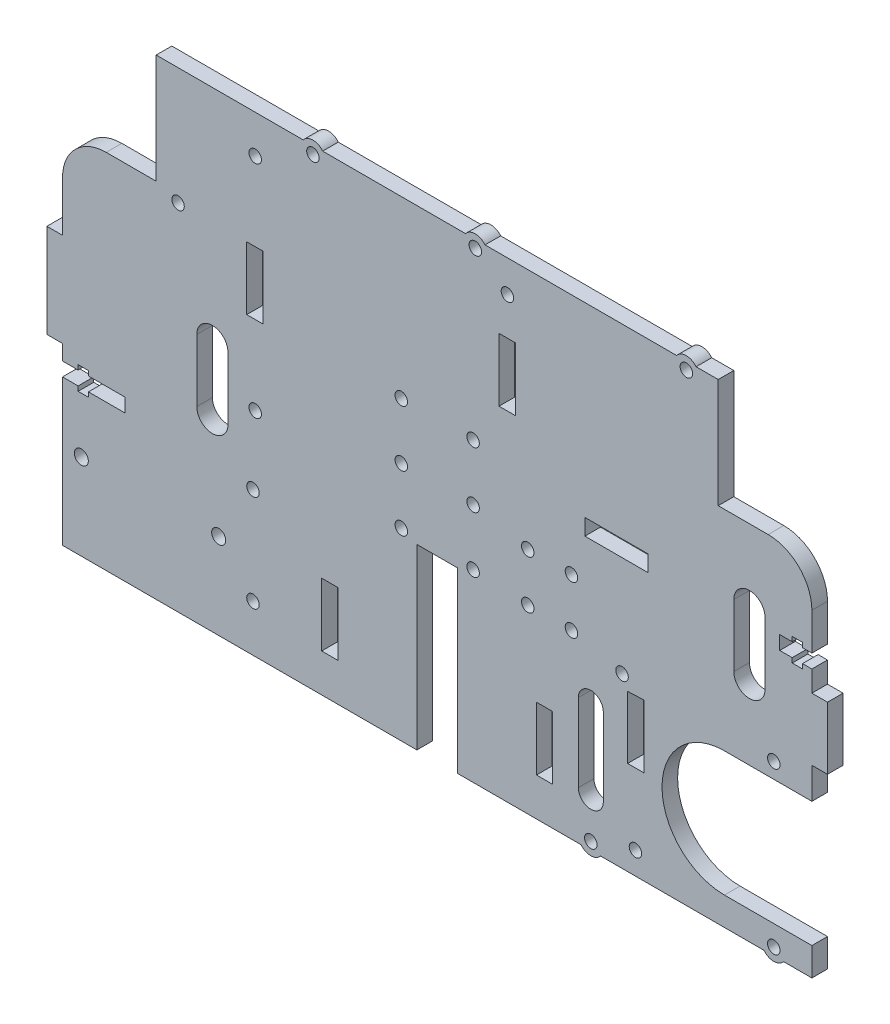
SolidWorks part; units mm, degrees
ref_plane "Front Plane" through (0, 0, 0) normal (0, 0, 1) x (1, 0, 0)
ref_plane "Top Plane" through (0, 0, 0) normal (0, 1, 0) x (1, 0, 0)
ref_plane "Right Plane" through (0, 0, 0) normal (1, 0, 0) x (0, 0, -1)
sketch "Sketch1" plane through (0, 0, 0) normal (0, 0, 1) x (1, 0, 0)
  line L1 (-120, 75.5) -> (120, 75.5)
  line L2 (-120, 75.5) -> (-120, -75.5)
  line L3 (-120, -75.5) -> (120, -75.5)
  line L4 (120, 75.5) -> (120, -75.5)
  dimension "D1" = 120
  dimension "D2" = 240
  dimension "D3" = 151
  dimension "D4" = 75.5
extrude "Boss-Extrude1" add sketch "Sketch1" along normal blind 5
sketch "Sketch2" plane through (0, 0, 0) normal (0, 0, -1) x (-1, 0, 0)
  line L0 (0, 0) -> (0, 57.3071) construction
  line L1 (0, 0) -> (-98.1862, 0) construction
  line L2 (-120, 75.5) -> (120, 75.5) construction
  line L3 (-60, 75.5) -> (50, 75.5)
  line L4 (-60, 75.5) -> (-60, 24.5)
  line L5 (-60, 24.5) -> (50, 24.5)
  line L6 (50, 75.5) -> (50, 24.5)
  dimension "D1" = 60
  dimension "D2" = 50
  dimension "D3" = 51
extrude "Cut-Extrude1" [suppressed] cut sketch "Sketch2" against normal blind 10
sketch "Sketch3" plane through (0, 0, 0) normal (0, 0, -1) x (-1, 0, 0)
  line L0 (0, 0) -> (0, -78.8573) construction
  line L2 (6.5, -75.5) -> (6.5, -18.5)
  line L3 (120, -75.5) -> (-120, -75.5) construction
  line L4 (-6.5, -75.5) -> (-6.5, -18.5)
  line L5 (6.5, -18.5) -> (-6.5, -18.5)
  line L6 (6.5, -75.5) -> (-6.5, -75.5)
  dimension "D1" = 6.5
  dimension "D2" = 6.5
  dimension "D3" = 57
extrude "Cut-Extrude2" cut sketch "Sketch3" against normal blind 10
sketch "Sketch5" plane through (0, 0, 0) normal (0, 0, -1) x (-1, 0, 0)
  line L0 (0, 0) -> (-50.5193, 0) construction
  line L1 (-31.8, -43.1) -> (-31.8, -63.3)
  line L2 (0, 0) -> (0, -33.9855) construction
  line L3 (-31.8, -43.1) -> (-37, -43.1)
  line L5 (-37, -43.1) -> (-37, -63.3)
  line L7 (-31.8, -63.3) -> (-37, -63.3)
  line L16 (31.8, -63.3) -> (37, -63.3)
  line L17 (37, -43.1) -> (37, -63.3)
  line L18 (31.8, -43.1) -> (37, -43.1)
  line L19 (31.8, -43.1) -> (31.8, -63.3)
  dimension "D1" = 5.2
  dimension "D2" = 20.2
  dimension "D3" = 37
  dimension "D4" = 43.1
extrude "Cut-Extrude4" cut sketch "Sketch5" against normal blind 10
sketch "Sketch6" plane through (0, 0, 0) normal (0, 0, -1) x (-1, 0, 0)
  line L0 (0, 0) -> (0, 25.6979) construction
  line L1 (0, 0) -> (-29.2256, 0) construction
  circle A1 centre (11.5, 19.5) radius 2
  circle A3 centre (11.5, 1.5) radius 2
  circle A5 centre (11.5, -16.5) radius 2
  circle A6 centre (-11.5, -16.5) radius 2
  circle A7 centre (-11.5, 1.5) radius 2
  circle A8 centre (-11.5, 19.5) radius 2
  dimension "D1" = 4
  dimension "D2" = 4
  dimension "D3" = 4
  dimension "D4" = 11.5
  dimension "D5" = 19.5
  dimension "D6" = 18
  dimension "D7" = 18
extrude "Cut-Extrude5" cut sketch "Sketch6" against normal blind 10
sketch "Sketch7" plane through (0, 0, 0) normal (0, 0, -1) x (-1, 0, 0)
  line L0 (0, 0) -> (0, -14.6108) construction
  line L1 (-36, -2.1) -> (-36, -21.1184) construction
  line L2 (0, 0) -> (-17.8652, 0) construction
  circle A1 centre (-43, -2.1) radius 2
  circle A3 centre (-43, -17.6) radius 2
  circle A8 centre (-29, -17.6) radius 2
  circle A9 centre (-29, -2.1) radius 2
  dimension "D3" = 4
  dimension "D4" = 4
  dimension "D5" = 15.5
  dimension "D6" = 4.2
  dimension "D1" = 36
  dimension "D2" = 7
extrude "Cut-Extrude6" cut sketch "Sketch7" against normal blind 10
sketch "Sketch8" plane through (0, 0, 0) normal (0, 0, -1) x (-1, 0, 0)
  line L0 (-120, -26.5) -> (-92, -26.5)
  line L1 (-120, -75.5) -> (-120, 75.5) construction
  line L2 (-120, -66.5) -> (-92, -66.5)
  line L3 (-6.5, -75.5) -> (-120, -75.5) construction
  line L4 (-120, -26.5) -> (-120, -66.5)
  arc A0 (-92, -26.5) -> (-92, -66.5) centre (-92, -46.5) cw
  dimension "D1" = 28
  dimension "D2" = 40
  dimension "D3" = 9
extrude "Cut-Extrude7" cut sketch "Sketch8" against normal blind 10
sketch "Sketch9" plane through (0, 0, 0) normal (0, 0, -1) x (-1, 0, 0)
  line L1 (0, 0) -> (-30.7701, 0) construction
  line L3 (0, 0) -> (0, -53.9951) construction
  circle A0 centre (-59.2, -21.5) radius 2
  circle A1 centre (-107.8, -21.5) radius 2
  circle A2 centre (-49.2, -73) radius 2
  circle A3 centre (-107.8, -73) radius 2
  dimension "D1" = 4
  dimension "D2" = 4
  dimension "D3" = 4
  dimension "D4" = 4
  dimension "D7" = 48.6
  dimension "D10" = 58.6
  dimension "D5" = 59.2
  dimension "D6" = 21.5
  dimension "D8" = 49.2
  dimension "D9" = 73
extrude "Cut-Extrude8" cut sketch "Sketch9" against normal blind 10
sketch "Sketch10" plane through (0, 0, 0) normal (0, 0, -1) x (-1, 0, 0)
  circle A0 centre (-107.8, -73) radius 2
  circle A1 centre (-107.8, -73) radius 4
  circle A2 centre (-49.2, -73) radius 2
  circle A3 centre (-49.2, -73) radius 4
  dimension "D1" = 4
  dimension "D2" = 8
  dimension "D3" = 4
  dimension "D4" = 8
extrude "Boss-Extrude2" add sketch "Sketch10" against normal blind 5
sketch "Sketch11" plane through (0, 0, 5) normal (0, 0, 1) x (1, 0, 0)
  line L1 (0, 0) -> (0, 50.8583) construction
  line L5 (0, 0) -> (-51.0189, 0) construction
  circle A0 centre (-24.8, 29.5) radius 2
  circle A1 centre (24.8, 29.5) radius 2
  dimension "D1" = 4
  dimension "D2" = 4
  dimension "D4" = 29.5
  dimension "D3" = 24.8
  dimension "D5" = 24.8
extrude "Cut-Extrude9" [suppressed] cut sketch "Sketch11" against normal blind 10
sketch "Sketch12" plane through (0, 0, 0) normal (0, 0, -1) x (-1, 0, 0)
  line L0 (-49.2, -35.1071) -> (-49.2, -60.1071) construction
  line L1 (-45.2, -35.1071) -> (-45.2, -60.1071)
  line L2 (-53.2, -35.1071) -> (-53.2, -60.1071)
  line L3 (-49.2, -71) -> (-49.2, -25.3616) construction
  arc A0 (-45.2, -35.1071) -> (-53.2, -35.1071) centre (-49.2, -35.1071) ccw
  arc A1 (-53.2, -60.1071) -> (-45.2, -60.1071) centre (-49.2, -60.1071) ccw
  circle A2 centre (-49.2, -73) radius 2 construction
  point P2 (-49.2, -47.6071)
  dimension "D1" = 8
  dimension "D2" = 25
extrude "Cut-Extrude10" cut sketch "Sketch12" against normal blind 10
sketch "Sketch13" plane through (0, 0, 0) normal (0, 0, -1) x (-1, 0, 0)
  line L0 (0, 0) -> (0, 120.0783) construction
  line L1 (-120, 75.5) -> (-90, 75.5)
  line L2 (-120, 75.5) -> (-120, 40.5)
  line L3 (-120, 40.5) -> (-90, 40.5)
  line L4 (-90, 75.5) -> (-90, 40.5)
  line L5 (90, 75.5) -> (90, 40.5)
  line L6 (120, 40.5) -> (90, 40.5)
  line L7 (120, 75.5) -> (120, 40.5)
  line L8 (120, 75.5) -> (90, 75.5)
  dimension "D1" = 30
  dimension "D2" = 35
extrude "Cut-Extrude11" cut sketch "Sketch13" against normal blind 10
sketch "Sketch14" plane through (0, 0, 0) normal (0, 0, -1) x (-1, 0, 0)
  line L1 (0, 0) -> (0, 60.6425) construction
  line L3 (0, 0) -> (51.7242, 0) construction
  circle A0 centre (-22.5, 65.3) radius 2
  circle A3 centre (-22.5, 20.7) radius 2
  dimension "D1" = 4
  dimension "D2" = 4
  dimension "D9" = 44.6
  dimension "D7" = 22.5
  dimension "D8" = 20.7
extrude "Cut-Extrude12" [suppressed] cut sketch "Sketch14" against normal blind 10
sketch "Sketch16" plane through (0, 0, 0) normal (0, 0, -1) x (-1, 0, 0)
  line L0 (0, 0) -> (67.1487, 0) construction
  line L1 (0, 0) -> (0, -41.5882) construction
  circle A1 centre (59, -29.5) radius 2
  circle A3 centre (59, -60.5) radius 2
  dimension "D1" = 4
  dimension "D2" = 4
  dimension "D5" = 31
  dimension "D3" = 29.5
  dimension "D4" = 59
extrude "Cut-Extrude13" cut sketch "Sketch16" against normal blind 5
sketch "Sketch17" plane through (0, 0, 0) normal (0, 0, -1) x (-1, 0, 0)
  line L0 (-100, 17) -> (-100, -3) construction
  line L1 (-95, 17) -> (-95, -3)
  line L2 (-105, 17) -> (-105, -3)
  line L4 (-120, 7) -> (-88.2409, 7) construction
  line L5 (-120, -26.5) -> (-120, 40.5) construction
  arc A0 (-95, 17) -> (-105, 17) centre (-100, 17) ccw
  arc A1 (-105, -3) -> (-95, -3) centre (-100, -3) ccw
  point P2 (-100, 7)
  dimension "D1" = 10
  dimension "D2" = 20
  dimension "D3" = 15
extrude "Cut-Extrude14" cut sketch "Sketch17" against normal blind 5
sketch "Sketch18" plane through (0, 0, 0) normal (0, 0, -1) x (-1, 0, 0)
  line L0 (72, -15.5) -> (72, 4.5) construction
  line L1 (67, -15.5) -> (67, 4.5)
  line L2 (77, -15.5) -> (77, 4.5)
  line L5 (0, 0) -> (0, 30.7987) construction
  line L6 (0, 0) -> (40.6403, 0) construction
  arc A0 (67, -15.5) -> (77, -15.5) centre (72, -15.5) ccw
  arc A1 (77, 4.5) -> (67, 4.5) centre (72, 4.5) ccw
  point P2 (72, -5.5)
  dimension "D4" = 20
  dimension "D1" = 72
  dimension "D2" = 10
  dimension "D3" = 4.5
extrude "Cut-Extrude15" cut sketch "Sketch18" against normal blind 5
sketch "Sketch19" plane through (0, 0, 0) normal (0, 0, -1) x (-1, 0, 0)
  line L0 (23, 20.5) -> (23, 40.5) construction
  line L1 (18, 20.5) -> (18, 40.5)
  line L2 (28, 20.5) -> (28, 40.5)
  line L5 (0, 0) -> (0, 49.6195) construction
  line L6 (0, 0) -> (50, 0) construction
  arc A0 (18, 20.5) -> (28, 20.5) centre (23, 20.5) ccw
  arc A1 (28, 40.5) -> (18, 40.5) centre (23, 40.5) ccw
  point P2 (23, 30.5)
  dimension "D1" = 10
  dimension "D2" = 23
  dimension "D3" = 20
  dimension "D4" = 20.5
extrude "Cut-Extrude16" [suppressed] cut sketch "Sketch19" against normal blind 10
sketch "Sketch20" plane through (0, 0, 0) normal (0, 0, -1) x (-1, 0, 0)
  line L1 (60.9956, 18) -> (60.9956, 38.2)
  line L3 (60.9956, 18) -> (55.7956, 18)
  line L6 (55.7956, 18) -> (55.7956, 38.2)
  line L7 (60.9956, 38.2) -> (55.7956, 38.2)
  line L8 (0, 0) -> (0, 33.2819) construction
  line L9 (0, 0) -> (33.8288, 0) construction
  dimension "D1" = 18
  dimension "D2" = 5.2
  dimension "D3" = 20.2
  dimension "D4" = 55.7956
extrude "Cut-Extrude17" cut sketch "Sketch20" against normal blind 10
sketch "Sketch21" plane through (0, 0, 0) normal (0, 0, -1) x (-1, 0, 0)
  line L1 (0, 0) -> (0, 47.6704) construction
  line L3 (0, 0) -> (36.5305, 0) construction
  circle A0 centre (58.2956, -7.3) radius 2
  circle A1 centre (58.2956, 63.3) radius 2
  dimension "D1" = 4
  dimension "D2" = 4
  dimension "D3" = 7.3
  dimension "D5" = 58.2956
  dimension "D4" = 58.2956
  dimension "D6" = 63.3
extrude "Cut-Extrude18" cut sketch "Sketch21" against normal blind 10
sketch "Sketch24" plane through (0, 0, 5) normal (0, 0, 1) x (1, 0, 0)
  line L8 (66.2, -45.5) -> (66.1962, -25.3)
  line L9 (66.1962, -25.3) -> (61, -25.5)
  line L10 (61, -25.5) -> (61, -45.5)
  line L11 (61, -45.5) -> (66.2, -45.5)
  dimension "D1" = 5.2
  dimension "D2" = 20.2
extrude "Cut-Extrude20" cut sketch "Sketch24" against normal blind 5
sketch "Sketch25" plane through (0, 0, 0) normal (0, 0, -1) x (-1, 0, 0)
  circle A0 centre (-63.5, -68.3) radius 2
  dimension "D1" = 4
extrude "Cut-Extrude21" cut sketch "Sketch25" against normal blind 5
sketch "Sketch26" plane through (0, 0, 0) normal (0, 0, -1) x (-1, 0, 0)
  circle A0 centre (39.8, 73) radius 2
  circle A1 centre (-12.2, 73) radius 2
  dimension "D1" = 4
  dimension "D2" = 4
extrude "Cut-Extrude22" cut sketch "Sketch26" against normal blind 10
sketch "Sketch27" plane through (0, 0, 0) normal (0, 0, -1) x (-1, 0, 0)
  circle A0 centre (39.8, 73) radius 2
  circle A1 centre (39.8, 73) radius 4
  circle A2 centre (-12.2, 73) radius 4
  circle A3 centre (-12.2, 73) radius 2
  dimension "D1" = 8
  dimension "D2" = 8
  dimension "D3" = 4
  dimension "D4" = 4
extrude "Boss-Extrude4" add sketch "Sketch27" against normal blind 5
fillet "Fillet1" radius 14 2 edges at (120, 40.5, 2.5) (-120, 40.5, 2.5)
sketch "Sketch28" plane through (0, 0, 5) normal (0, 0, 1) x (1, 0, 0)
  line L8 (25, 33) -> (25, 53.2)
  line L9 (25, 53.2) -> (19.8, 53.2)
  line L10 (19.8, 53.2) -> (19.8, 33)
  line L11 (19.8, 33) -> (25, 33)
  dimension "D1" = 20.2
  dimension "D2" = 5.2
extrude "Cut-Extrude23" cut sketch "Sketch28" against normal blind 5
sketch "Sketch29" plane through (0, 0, 5) normal (0, 0, 1) x (1, 0, 0)
  line L8 (47.3, 10.7) -> (67.5, 10.7)
  line L9 (67.5, 10.7) -> (67.5, 15.9)
  line L10 (67.5, 15.9) -> (47.3, 15.9)
  line L11 (47.3, 15.9) -> (47.3, 10.7)
  dimension "D1" = 5.2
  dimension "D2" = 20.2
extrude "Cut-Extrude24" cut sketch "Sketch29" against normal blind 5
sketch "Sketch30" plane through (0, 0, 0) normal (0, 0, -1) x (-1, 0, 0)
  circle A0 centre (-79.8, 73) radius 2
  dimension "D1" = 4
extrude "Cut-Extrude25" cut sketch "Sketch30" against normal blind 5
sketch "Sketch31" plane through (0, 0, 0) normal (0, 0, -1) x (-1, 0, 0)
  circle A0 centre (-79.8, 73) radius 2
  circle A1 centre (-79.8, 73) radius 4
  dimension "D1" = 8
extrude "Boss-Extrude5" add sketch "Sketch31" against normal blind 5
sketch "Sketch32" plane through (0, 0, 0) normal (0, 0, -1) x (-1, 0, 0)
  circle A0 centre (83, 38) radius 2
  dimension "D1" = 4
extrude "Cut-Extrude26" cut sketch "Sketch32" against normal blind 5
sketch "Sketch33" plane through (0, 0, 0) normal (0, 0, -1) x (-1, 0, 0)
  line L0 (120, 26.5) -> (120, -75.5) construction
  line L5 (-120, -26.5) -> (-120, 26.5) construction
  line L6 (120, -19.5) -> (125, -19.5)
  line L7 (120, -19.5) -> (120, 10.5)
  line L8 (120, 10.5) -> (125, 10.5)
  line L9 (125, -19.5) -> (125, 10.5)
  line L10 (-120, 3.5) -> (-125, 3.5)
  line L11 (-120, 3.5) -> (-120, -16.5)
  line L12 (-120, -16.5) -> (-125, -16.5)
  line L13 (-125, 3.5) -> (-125, -16.5)
  line L15 (90, 40.5) -> (106, 40.5) construction
  line L16 (-92, -26.5) -> (-120, -26.5) construction
  dimension "D4" = 30
  dimension "D5" = 30
  dimension "D6" = 5
  dimension "D7" = 5
  dimension "D8" = 10
  dimension "D9" = 20
extrude "Boss-Extrude6" add sketch "Sketch33" against normal blind 5
sketch "Sketch34" plane through (0, 0, 0) normal (0, 0, -1) x (-1, 0, 0)
  circle A1 centre (113.98, -48) radius 2.25
  circle A3 centre (69.98, -48) radius 2.25
extrude "Cut-Extrude27" cut sketch "Sketch34" against normal blind 5
sketch "Sketch35" plane through (0, 0, 0) normal (0, 0, -1) x (-1, 0, 0)
  line L0 (-119.8939, 12.4056) -> (-90.0212, 12.4056) construction
  line L1 (-120, 14.6056) -> (-117, 14.6056)
  line L2 (-117, 14.6056) -> (-117, 16.1056)
  line L3 (-117, 16.1056) -> (-113.7, 16.1056)
  line L4 (-113.7, 16.1056) -> (-113.7, 14.6056)
  line L5 (-113.7, 14.6056) -> (-109.7051, 14.6056)
  line L6 (-109.7051, 14.6056) -> (-109.7051, 10.2056)
  line L7 (-109.7051, 10.2056) -> (-113.7, 10.2056)
  line L8 (-113.7, 10.2056) -> (-113.7, 8.7056)
  line L9 (-113.7, 8.7056) -> (-117, 8.7056)
  line L10 (-117, 8.7056) -> (-117, 10.2056)
  line L11 (-117, 10.2056) -> (-120, 10.2056)
  line L12 (-120, 10.2056) -> (-120, 14.6056)
  line L13 (-120, 3.5) -> (-120, 26.5) construction
  line L14 (106.7, -26.5785) -> (136.5727, -26.5785) construction
  line L15 (100, -24.3785) -> (111.7, -24.3785)
  line L16 (111.7, -24.3785) -> (111.7, -22.8785)
  line L17 (111.7, -22.8785) -> (115, -22.8785)
  line L18 (115, -22.8785) -> (115, -24.3785)
  line L19 (115, -24.3785) -> (120, -24.3785)
  line L20 (120, -24.3785) -> (120, -28.7785)
  line L21 (120, -28.7785) -> (115, -28.7785)
  line L22 (115, -28.7785) -> (115, -30.2785)
  line L23 (115, -30.2785) -> (111.7, -30.2785)
  line L24 (111.7, -30.2785) -> (111.7, -28.7785)
  line L25 (111.7, -28.7785) -> (100, -28.7785)
  line L26 (100, -28.7785) -> (100, -24.3785)
  line L27 (120, -19.5) -> (120, -75.5) construction
  dimension "D1" = 4.4
  dimension "D2" = 1.5
  dimension "D3" = 3.3
  dimension "D4" = 3
  dimension "D5" = 4.4
  dimension "D6" = 1.5
  dimension "D7" = 3.3
  dimension "D8" = 5
  dimension "D9" = 20
extrude "Cut-Extrude28" cut sketch "Sketch35" against normal blind 5
sketch "Sketch36" plane through (0, 0, 0) normal (0, 0, -1) x (-1, 0, 0)
  circle A0 centre (-22.5, 65.3) radius 2
  dimension "D1" = 4
extrude "Cut-Extrude29" cut sketch "Sketch36" against normal blind 5
